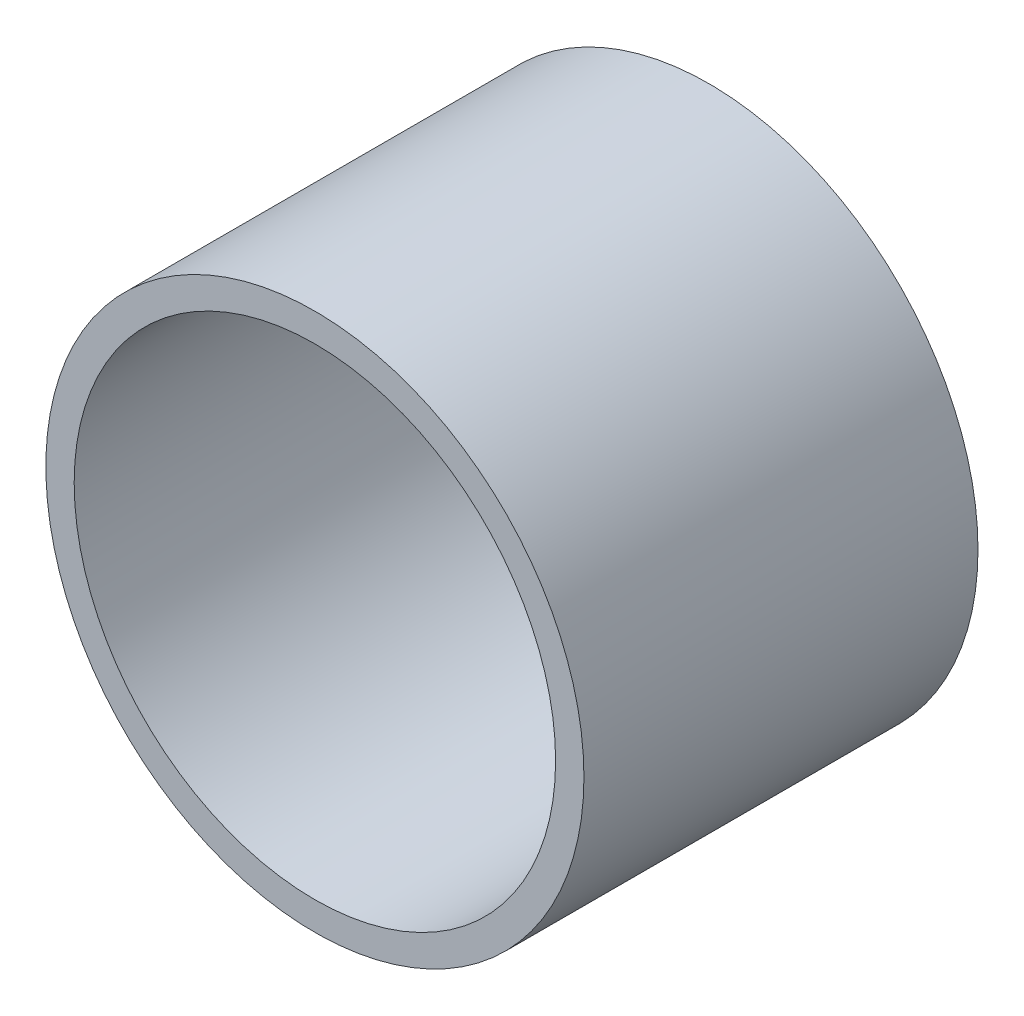
SolidWorks part; units mm, degrees
ref_plane "Front Plane" through (0, 0, 0) normal (0, 0, 1) x (1, 0, 0)
ref_plane "Top Plane" through (0, 0, 0) normal (0, 1, 0) x (1, 0, 0)
ref_plane "Right Plane" through (0, 0, 0) normal (1, 0, 0) x (0, 0, -1)
sketch "Sketch1" plane through (0, 0, 0) normal (0, 0, 1) x (1, 0, 0)
  circle A0 centre (0, 0) radius 57.15
  dimension "Pipe OD" = 114.3
extrude "Extrude-Thin1" add sketch "Sketch1" along normal mid plane 83.7 thin thin type one direction reverse wall 6.0198
